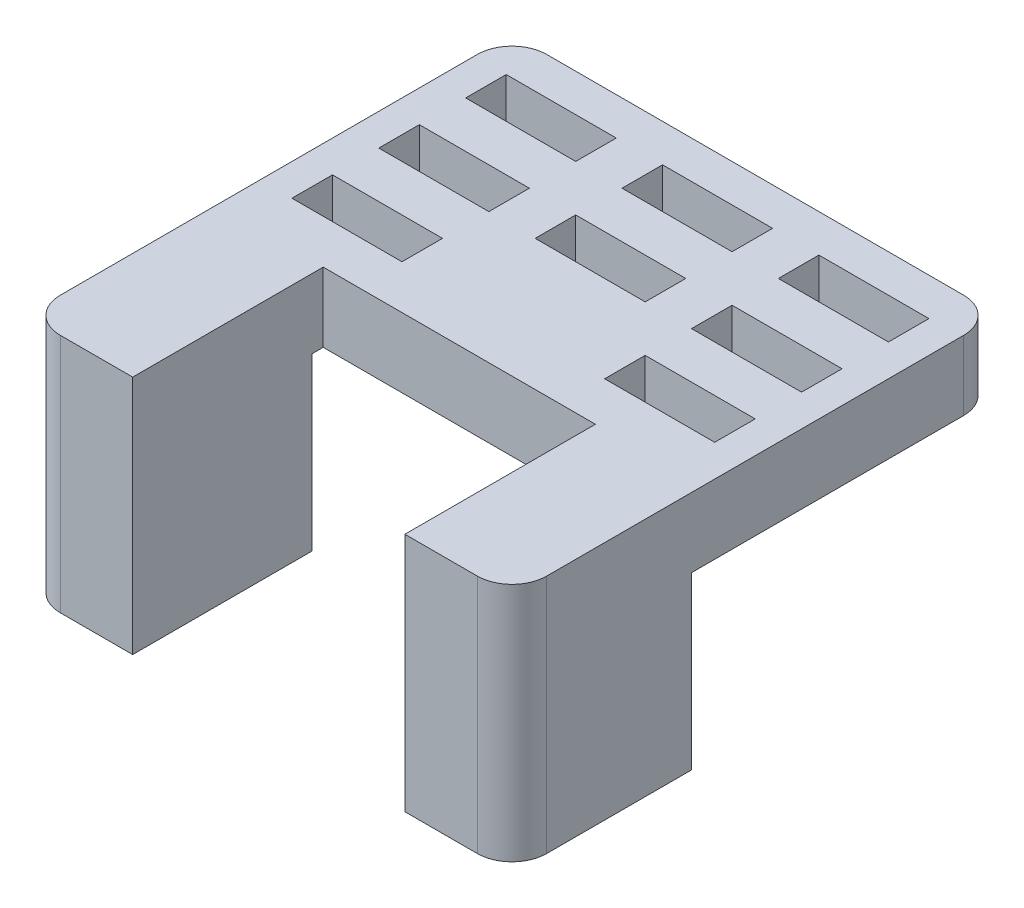
SolidWorks part; units mm, degrees
ref_plane "Front Plane" through (0, 0, 0) normal (0, 0, 1) x (1, 0, 0)
ref_plane "Top Plane" through (0, 0, 0) normal (0, 1, 0) x (1, 0, 0)
ref_plane "Right Plane" through (0, 0, 0) normal (1, 0, 0) x (0, 0, -1)
sketch "Sketch1" plane through (0, 0, 0) normal (0, 1, 0) x (1, 0, 0)
  line L1 (0, 0) -> (44, 0)
  line L2 (0, 0) -> (0, 44)
  line L3 (0, 44) -> (44, 44)
  line L4 (44, 0) -> (44, 44)
  dimension "D1" = 44
extrude "Boss-Extrude1" add sketch "Sketch1" against normal blind 6 contours L3 L4 L1 L2
sketch "Sketch2" plane through (0, 0, 0) normal (0, 1, 0) x (1, 0, 0)
  line L0 (5.475, 38) -> (11.525, 38) construction
  line L2 (0, 44) -> (44, 44) construction
  line L3 (0, 0) -> (0, 44) construction
  line L35 (18.975, 38) -> (25.025, 38) construction
  line L36 (5.475, 39.275) -> (11.525, 39.275)
  line L37 (5.475, 36.725) -> (11.525, 36.725)
  line L40 (18.975, 39.275) -> (25.025, 39.275)
  line L41 (18.975, 36.725) -> (25.025, 36.725)
  line L42 (32.475, 38) -> (38.525, 38) construction
  line L43 (32.475, 39.275) -> (38.525, 39.275)
  line L44 (32.475, 36.725) -> (38.525, 36.725)
  line L45 (18.975, 30.5) -> (25.025, 30.5) construction
  line L46 (18.975, 31.775) -> (25.025, 31.775)
  line L47 (18.975, 29.225) -> (25.025, 29.225)
  line L48 (32.475, 30.5) -> (38.525, 30.5) construction
  line L49 (32.475, 31.775) -> (38.525, 31.775)
  line L50 (32.475, 29.225) -> (38.525, 29.225)
  line L54 (32.475, 23) -> (38.525, 23) construction
  line L55 (32.475, 24.275) -> (38.525, 24.275)
  line L56 (32.475, 21.725) -> (38.525, 21.725)
  line L57 (5.475, 30.5) -> (11.525, 30.5) construction
  line L58 (5.475, 31.775) -> (11.525, 31.775)
  line L59 (5.475, 29.225) -> (11.525, 29.225)
  line L60 (5.475, 23) -> (11.525, 23) construction
  line L61 (5.475, 24.275) -> (11.525, 24.275)
  line L62 (5.475, 21.725) -> (11.525, 21.725)
  line L63 (18.975, 23) -> (25.025, 23) construction
  line L64 (18.975, 24.275) -> (25.025, 24.275)
  line L65 (18.975, 21.725) -> (25.025, 21.725)
  line L66 (18.975, 23) -> (25.025, 23) construction
  line L67 (18.975, 24.275) -> (25.025, 24.275)
  line L68 (18.975, 21.725) -> (25.025, 21.725)
  arc A0 (5.475, 39.275) -> (5.475, 36.725) centre (5.475, 38) ccw
  arc A1 (11.525, 36.725) -> (11.525, 39.275) centre (11.525, 38) ccw
  arc A2 (18.975, 39.275) -> (18.975, 36.725) centre (18.975, 38) ccw
  arc A3 (25.025, 36.725) -> (25.025, 39.275) centre (25.025, 38) ccw
  arc A4 (32.475, 39.275) -> (32.475, 36.725) centre (32.475, 38) ccw
  arc A5 (38.525, 36.725) -> (38.525, 39.275) centre (38.525, 38) ccw
  arc A6 (18.975, 31.775) -> (18.975, 29.225) centre (18.975, 30.5) ccw
  arc A7 (25.025, 29.225) -> (25.025, 31.775) centre (25.025, 30.5) ccw
  arc A8 (32.475, 31.775) -> (32.475, 29.225) centre (32.475, 30.5) ccw
  arc A9 (38.525, 29.225) -> (38.525, 31.775) centre (38.525, 30.5) ccw
  arc A12 (32.475, 24.275) -> (32.475, 21.725) centre (32.475, 23) ccw
  arc A13 (38.525, 21.725) -> (38.525, 24.275) centre (38.525, 23) ccw
  arc A14 (5.475, 31.775) -> (5.475, 29.225) centre (5.475, 30.5) ccw
  arc A15 (11.525, 29.225) -> (11.525, 31.775) centre (11.525, 30.5) ccw
  arc A16 (5.475, 24.275) -> (5.475, 21.725) centre (5.475, 23) ccw
  arc A17 (11.525, 21.725) -> (11.525, 24.275) centre (11.525, 23) ccw
  arc A20 (18.975, 24.275) -> (18.975, 21.725) centre (18.975, 23) ccw
  arc A21 (25.025, 21.725) -> (25.025, 24.275) centre (25.025, 23) ccw
  point P6 (8.5, 38)
  point P16 (22, 38)
  point P23 (35.5, 38)
  point P30 (22, 30.5)
  point P37 (35.5, 30.5)
  point P44 (22, 23)
  point P51 (35.5, 23)
  point P58 (8.5, 30.5)
  point P65 (8.5, 23)
  point P72 (22, 23)
  point P79 (22, 23)
  dimension "D1" = 2.55
  dimension "D2" = 6
  dimension "D3" = 8.5
  dimension "D4" = 6.05
  dimension "D5" = 3
  dimension "D6" = 3
extrude "Cut-Extrude1" cut sketch "Sketch2" against normal through all
sketch "Sketch4" plane through (0, -6, 0) normal (0, -1, 0) x (1, 0, 0)
  line L0 (0, 0) -> (0, -44) construction
  line L1 (44, 0) -> (0, 0)
  line L2 (44, 0) -> (44, -16.5)
  line L3 (44, -16.5) -> (0, -16.5)
  line L4 (0, 0) -> (0, -16.5)
  dimension "D1" = 16.5
extrude "Boss-Extrude2" add sketch "Sketch4" along normal blind 14.75
sketch "Sketch5" plane through (0, 0, 0) normal (0, 1, 0) x (1, 0, 0)
  line L0 (0, 0) -> (44, 0) construction
  line L1 (10.25, 0) -> (33.75, 0)
  line L2 (10.25, 0) -> (10.25, 17.45)
  line L3 (10.25, 17.45) -> (33.75, 17.45)
  line L4 (33.75, 0) -> (33.75, 17.45)
  point P8 (22, 0)
  dimension "D1" = 23.5
  dimension "D2" = 17.45
extrude "Cut-Extrude2" cut sketch "Sketch5" against normal through all
fillet "Fillet1" radius 3 4 edges at (44, -3, -44) (0, -3, -44) (0, -10.375, 0) (44, -10.375, 0)
other "Move Face1" [suppressed] parameters "D1"=9.23
sketch "Sketch6" plane through (0, 0, 0) normal (0, 1, 0) x (1, 0, 0)
  line L0 (13.25, 38) -> (12.8, 38) construction
  line L1 (13.25, 39.75) -> (3.75, 39.75)
  line L2 (13.25, 39.75) -> (13.25, 36.25)
  line L3 (13.25, 36.25) -> (3.75, 36.25)
  line L4 (3.75, 39.75) -> (3.75, 36.25)
  line L5 (8.5, 36.25) -> (8.5, 36.725) construction
  line L6 (5.475, 36.725) -> (11.525, 36.725) construction
  arc A1 (11.525, 36.725) -> (11.525, 39.275) centre (11.525, 38) ccw construction
  dimension "D1" = 3.5
  dimension "D2" = 9.5
extrude "Cut-Extrude3" cut sketch "Sketch6" against normal blind 3.52
pattern_linear "LPattern1" count 3 spacing 13.5 along (1, 0, 0) count 3 spacing 7.5 along (0, 0, 1) skipping (1, 2) of "Cut-Extrude3"
sketch "Sketch7" plane through (0, 0, 0) normal (0, 1, 0) x (1, 0, 0)
  line L0 (10.25, 0) -> (10.25, 1)
  line L1 (4, 43) -> (40, 43)
  line L2 (1, 40) -> (1, 4)
  line L3 (4, 1) -> (10.25, 1)
  line L4 (43, 40) -> (43, 4)
  line L5 (33.75, 0) -> (33.75, 1)
  line L6 (33.75, 1) -> (40, 1)
  line L41 (44, 3) -> (44, 41)
  line L42 (41, 44) -> (3, 44)
  line L43 (0, 41) -> (0, 3)
  line L44 (3, 0) -> (10.25, 0)
  line L45 (10.25, 0) -> (10.25, 17.45)
  line L46 (10.25, 17.45) -> (33.75, 17.45)
  line L47 (33.75, 17.45) -> (33.75, 0)
  line L48 (33.75, 0) -> (41, 0)
  line L49 (44, 3) -> (44, 41)
  line L50 (41, 44) -> (3, 44)
  line L51 (0, 41) -> (0, 3)
  line L52 (3, 0) -> (10.25, 0)
  line L56 (33.75, 0) -> (41, 0)
  arc A0 (1, 40) -> (4, 43) centre (4, 40) cw
  arc A1 (43, 40) -> (40, 43) centre (40, 40) ccw
  arc A2 (40, 1) -> (43, 4) centre (40, 4) ccw
  arc A3 (4, 1) -> (1, 4) centre (4, 4) cw
  arc A5 (44, 41) -> (41, 44) centre (41, 41) ccw
  arc A6 (3, 44) -> (0, 41) centre (3, 41) ccw
  arc A7 (0, 3) -> (3, 0) centre (3, 3) ccw
  arc A8 (41, 0) -> (44, 3) centre (41, 3) ccw
  arc A9 (44, 41) -> (41, 44) centre (41, 41) ccw
  arc A10 (3, 44) -> (0, 41) centre (3, 41) ccw
  arc A11 (0, 3) -> (3, 0) centre (3, 3) ccw
  arc A12 (41, 0) -> (44, 3) centre (41, 3) ccw
  dimension "D6" = 3
  dimension "D7" = 3
  dimension "D8" = 3
  dimension "D9" = 3
  dimension "D2" = 1
  dimension "D3" = 1
  dimension "D4" = 1
  dimension "D5" = 1
  dimension "D1" = 0
extrude "Cut-Extrude5" cut sketch "Sketch7" against normal up to next
